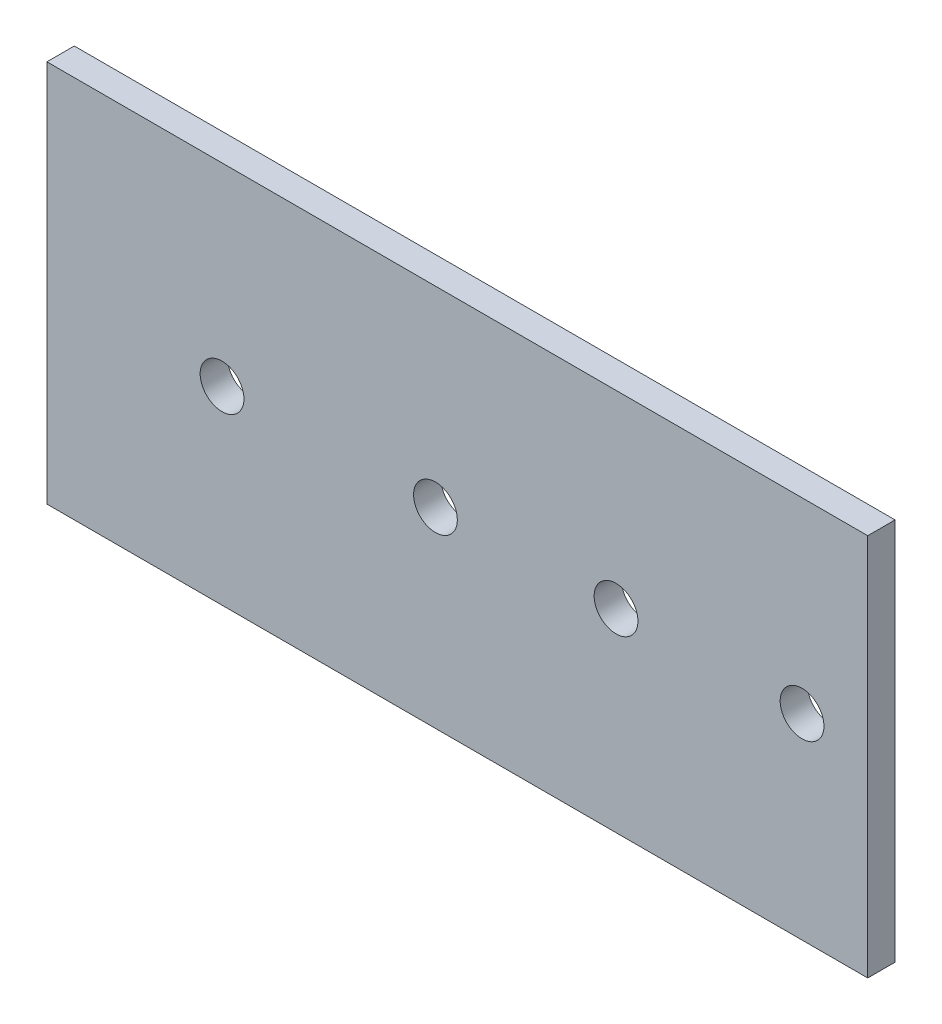
SolidWorks part; units mm, degrees
ref_plane "Front Plane" through (0, 0, 0) normal (0, 0, 1) x (1, 0, 0)
ref_plane "Top Plane" through (0, 0, 0) normal (0, 1, 0) x (1, 0, 0)
ref_plane "Right Plane" through (0, 0, 0) normal (1, 0, 0) x (0, 0, -1)
sketch "Sketch1" plane through (0, 0, 0) normal (0, 0, 1) x (1, 0, 0)
  line L1 (-75, -35) -> (75, -35)
  line L2 (-75, -35) -> (-75, 35)
  line L3 (-75, 35) -> (75, 35)
  line L4 (75, -35) -> (75, 35)
  line L5 (-75, -35) -> (75, 35) construction
  line L6 (-75, 35) -> (75, -35) construction
  point P0 (0, 0)
  dimension "D1" = 150
  dimension "D2" = 70
extrude "Boss-Extrude1" add sketch "Sketch1" along normal mid plane 5
sketch "Sketch2" plane through (0, 0, 2.5) normal (0, 0, 1) x (1, 0, 0)
  circle A0 centre (63, 0.8512) radius 4
  circle A1 centre (29.0022, 0.4608) radius 4
  circle A2 centre (-42.9953, -0.3659) radius 4
  circle A4 centre (-3.9971, 0) radius 4
  dimension "D1" = 8
  dimension "D2" = 8
  dimension "D3" = 8
  dimension "D4" = 8
extrude "Cut-Extrude1" cut sketch "Sketch2" against normal through all
